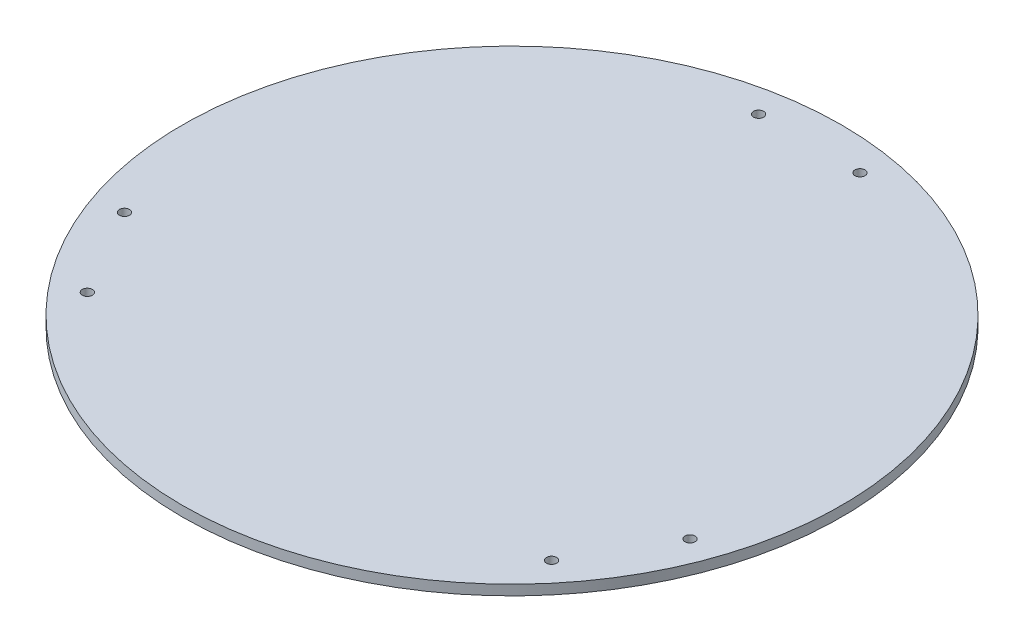
SolidWorks part; units mm, degrees
material "PE High Density"
ref_plane "Front Plane" through (0, 0, 0) normal (0, 0, 1) x (1, 0, 0)
ref_plane "Top Plane" through (0, 0, 0) normal (0, 1, 0) x (1, 0, 0)
ref_plane "Right Plane" through (0, 0, 0) normal (1, 0, 0) x (0, 0, -1)
sketch "Sketch1" plane through (0, 0, 0) normal (0, 1, 0) x (1, 0, 0)
  line L0 (0, 0) -> (0, 65) construction
  circle A0 centre (0, 0) radius 65
  circle A1 centre (0, 0) radius 59.48 construction
  circle A2 centre (-10, 58.6334) radius 1
  circle A3 centre (10, 58.6334) radius 1
  circle A4 centre (55.778, -20.6564) radius 1
  circle A5 centre (45.778, -37.9769) radius 1
  circle A6 centre (-45.778, -37.9769) radius 1
  circle A7 centre (-55.778, -20.6564) radius 1
  point P19 (0, 0)
  dimension "D1" = 130
  dimension "D2" = 118.96
  dimension "D3" = 2
  dimension "D4" = 10
  dimension "D5" = 3
extrude "Boss-Extrude1" add sketch "Sketch1" along normal blind 2
